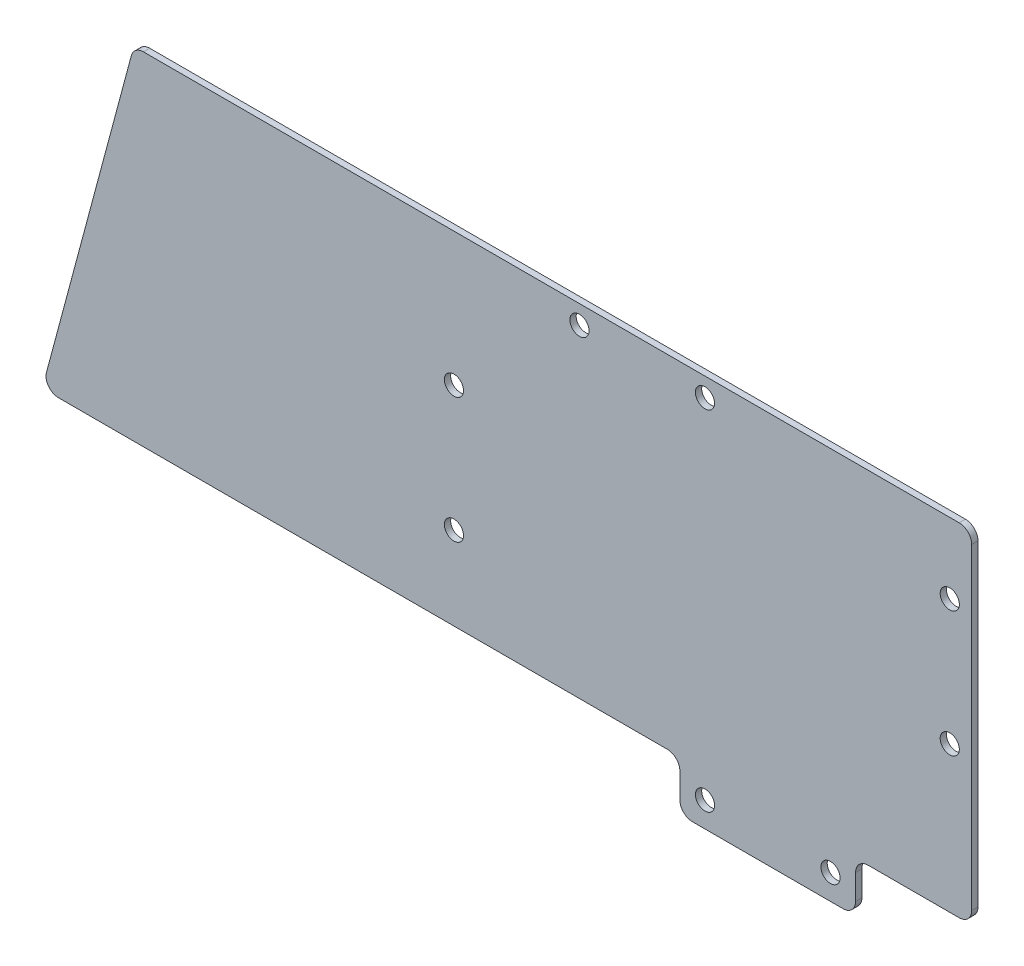
SolidWorks part; units mm, degrees
material "Thornel Mat VMA"
ref_plane "前视基准面" through (0, 0, 0) normal (0, 0, 1) x (1, 0, 0)
ref_plane "上视基准面" through (0, 0, 0) normal (0, 1, 0) x (1, 0, 0)
ref_plane "右视基准面" through (0, 0, 0) normal (1, 0, 0) x (0, 0, -1)
other "Configuration Table"
sketch "草图1" plane through (0, 0, 0) normal (0, 0, 1) x (1, 0, 0)
  line L0 (0, 0) -> (20, 0) construction
  line L2 (24, 4) -> (-4, 4)
  line L3 (24, 4) -> (24, -4)
  line L4 (24, -4) -> (-4, -4)
  line L5 (-4, 4) -> (-4, -4)
  line L6 (24, 4) -> (-4, -4) construction
  line L7 (24, -4) -> (-4, 4) construction
  line L8 (-45, 58.5) -> (42.5, 58.5)
  line L9 (-45, 58.5) -> (-45, 4)
  line L10 (-45, 4) -> (42.5, 4)
  line L11 (42.5, 58.5) -> (42.5, 4)
  circle A0 centre (0, 0) radius 1.525
  circle A1 centre (20, 0) radius 1.525
  point P5 (10, 0)
  dimension "D1" = 3.05
  dimension "D3" = 4
  dimension "D4" = 4
  dimension "D6" = 42.5
  dimension "D2" = 20
  dimension "D5" = 45
  dimension "D7" = 54.5
extrude "凸台-拉伸1" add sketch "草图1" along normal blind 1 contours L11 L8 L9 L10 L2 | L2 L5 L4 L3 A1 A0
sketch "草图2" plane through (0, 0, 1) normal (0, 0, 1) x (1, 0, 0)
  line L0 (-40, 47.25) -> (-40, 27.25) construction
  line L1 (-40, 27.25) -> (-40, 4) construction
  line L2 (-45, 4) -> (-4, 4) construction
  line L3 (-45, 58.5) -> (-45, 4) construction
  circle A0 centre (-40, 47.25) radius 1.525 construction
  circle A1 centre (-40, 27.25) radius 1.525 construction
  circle A2 centre (-40, 37.25) radius 1.525
  circle A3 centre (-40, 17.25) radius 1.525
  dimension "D1" = 3.05
  dimension "D5" = 20
  dimension "D2" = 20
  dimension "D3" = 23.25
  dimension "D4" = 5
extrude "切除-拉伸1" cut sketch "草图2" against normal blind 1
fillet "圆角1" radius 2 8 edges at (42.5, 4, 0.5) (24, 4, 0.5) (24, -4, 0.5) (-4, -4, 0.5) (-4, 4, 0.5) (-45, 4, 0.5) (42.5, 58.5, 0.5) (-45, 58.5, 0.5)
sketch "草图3" plane through (0, 0, 1) normal (0, 0, 1) x (1, 0, 0)
  line L0 (42.5, 56.5) -> (42.5, 6) construction
  line L1 (-33, 47.25) -> (39, 47.25) construction
  line L2 (-33, 47.25) -> (-33, 27.25) construction
  line L3 (-33, 27.25) -> (39, 27.25) construction
  line L4 (39, 47.25) -> (39, 27.25) construction
  circle A0 centre (39, 47.25) radius 1.525
  circle A1 centre (39, 27.25) radius 1.525
  circle A2 centre (-40, 37.25) radius 1.525 construction
  dimension "D1" = 3.5
  dimension "D2" = 20
  dimension "D3" = 27.25
  dimension "D4" = 72
extrude "切除-拉伸2" cut sketch "草图3" against normal blind 10
sketch "草图4" plane through (0, 0, 1) normal (0, 0, 1) x (1, 0, 0)
  line L0 (-20, 55.5) -> (0, 55.5) construction
  line L1 (-43, 58.5) -> (40.5, 58.5) construction
  line L2 (-45, 56.5) -> (-45, 6) construction
  circle A0 centre (-20, 55.5) radius 1.525
  circle A1 centre (0, 55.5) radius 1.525
  circle A2 centre (39, 47.25) radius 1.525 construction
  dimension "D1" = 20
  dimension "D2" = 3
  dimension "D3" = 25
extrude "切除-拉伸3" cut sketch "草图4" against normal blind 10
sketch "草图5" plane through (0, 0, 1) normal (0, 0, 1) x (1, 0, 0)
  line L0 (-43, 58.5) -> (-91, 58.5)
  line L1 (-91, 58.5) -> (-105.6032, 4)
  line L2 (-105.6032, 4) -> (-43, 4)
  line L3 (-91, 58.5) -> (-91, 4) construction
  line L11 (26, 4) -> (40.5, 4)
  line L12 (42.5, 6) -> (42.5, 56.5)
  line L13 (40.5, 58.5) -> (-43, 58.5)
  line L14 (-45, 56.5) -> (-45, 6)
  line L15 (-43, 4) -> (-6, 4)
  line L16 (-4, 2) -> (-4, -2)
  line L17 (-2, -4) -> (22, -4)
  line L18 (24, -2) -> (24, 2)
  line L19 (26, 4) -> (40.5, 4)
  line L20 (42.5, 6) -> (42.5, 56.5)
  line L21 (40.5, 58.5) -> (-43, 58.5)
  line L22 (-45, 56.5) -> (-45, 6)
  line L23 (-43, 4) -> (-6, 4)
  line L24 (-4, 2) -> (-4, -2)
  line L25 (-2, -4) -> (22, -4)
  line L26 (24, -2) -> (24, 2)
  arc A8 (40.5, 4) -> (42.5, 6) centre (40.5, 6) ccw
  arc A9 (42.5, 56.5) -> (40.5, 58.5) centre (40.5, 56.5) ccw
  arc A10 (-43, 58.5) -> (-45, 56.5) centre (-43, 56.5) ccw
  arc A11 (-45, 6) -> (-43, 4) centre (-43, 6) ccw
  arc A12 (-4, 2) -> (-6, 4) centre (-6, 2) ccw
  arc A13 (-4, -2) -> (-2, -4) centre (-2, -2) ccw
  arc A14 (22, -4) -> (24, -2) centre (22, -2) ccw
  arc A15 (26, 4) -> (24, 2) centre (26, 2) ccw
  arc A16 (40.5, 4) -> (42.5, 6) centre (40.5, 6) ccw
  arc A17 (42.5, 56.5) -> (40.5, 58.5) centre (40.5, 56.5) ccw
  arc A18 (-43, 58.5) -> (-45, 56.5) centre (-43, 56.5) ccw
  arc A19 (-45, 6) -> (-43, 4) centre (-43, 6) ccw
  arc A20 (-4, 2) -> (-6, 4) centre (-6, 2) ccw
  arc A21 (-4, -2) -> (-2, -4) centre (-2, -2) ccw
  arc A22 (22, -4) -> (24, -2) centre (22, -2) ccw
  arc A23 (26, 4) -> (24, 2) centre (26, 2) ccw
  arc M28 (-43, 58.5) -> (-45, 56.5) centre (-43, 56.5) ccw
  line M29 (-45, 56.5) -> (-45, 6)
  arc M30 (-45, 6) -> (-43, 4) centre (-43, 6) ccw
  dimension "D2" = 15
  dimension "D3" = 48
  dimension "D1" = 0
extrude "凸台-拉伸2" add sketch "草图5" against normal up to surface (1 mm away) contours L0 L3 L2 M30 M29 M28 | L3 L1 L2
fillet "圆角2" radius 2 2 edges at (-105.6032, 4, 0.5) (-91, 58.5, 0.5)
